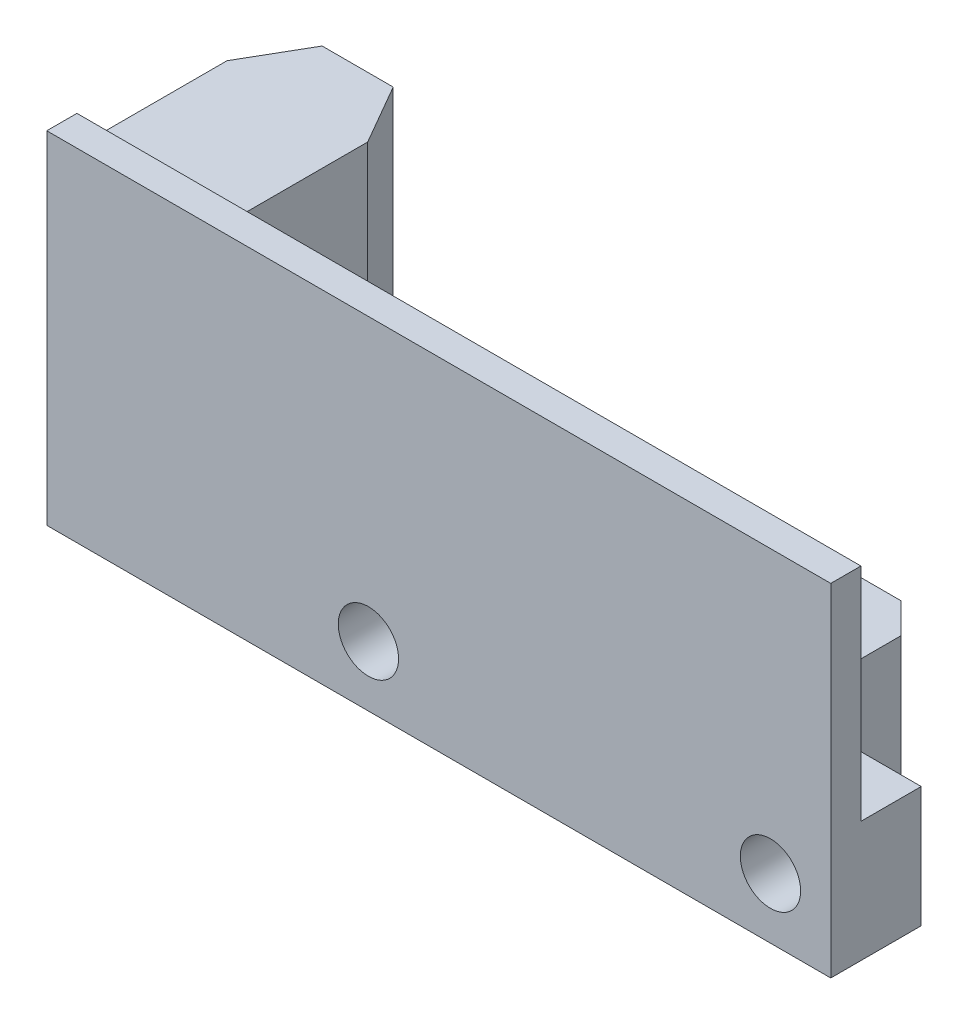
SolidWorks part; units mm, degrees
ref_plane "Plan de face" through (0, 0, 0) normal (0, 0, 1) x (1, 0, 0)
ref_plane "Plan de dessus" through (0, 0, 0) normal (0, 1, 0) x (1, 0, 0)
ref_plane "Plan de droite" through (0, 0, 0) normal (1, 0, 0) x (0, 0, -1)
sketch "Esquisse1" plane through (0, 0, 0) normal (0, 0, 1) x (1, 0, 0)
  line L1 (-19.5, 8.5) -> (19.5, 8.5)
  line L2 (-19.5, 8.5) -> (-19.5, -8.5)
  line L3 (-19.5, -8.5) -> (19.5, -8.5)
  line L4 (19.5, 8.5) -> (19.5, -8.5)
  line L5 (-19.5, 8.5) -> (19.5, -8.5) construction
  line L6 (-19.5, -8.5) -> (19.5, 8.5) construction
  point P0 (0, 0)
  dimension "D1" = 39
  dimension "D2" = 17
extrude "Boss.-Extru.1" add sketch "Esquisse1" along normal blind 1.5
sketch "Esquisse3" plane through (0, -8.5, 0) normal (0, 1, 0) x (1, 0, 0)
  line L0 (19.5, 0) -> (19.5, 3)
  line L1 (19.5, 3) -> (12.5, 3)
  line L2 (12.5, 3) -> (12.5, 10.5)
  line L3 (12.5, 10.5) -> (8.5, 10.5)
  line L4 (8.5, 10.5) -> (8.5, 3)
  line L5 (8.5, 3) -> (5.5, 3)
  line L6 (5.5, 3) -> (5.5, 10.5)
  line L7 (5.5, 10.5) -> (1.5, 10.5)
  line L8 (1.5, 10.5) -> (1.5, 3)
  line L9 (1.5, 3) -> (-5.5, 3)
  line L10 (-5.5, 3) -> (-5.5, 0)
  line L11 (19.5, 0) -> (-19.5, 0) construction
  line L12 (-5.5, 0) -> (19.5, 0)
  dimension "D1" = 25
  dimension "D2" = 3
  dimension "D3" = 4
  dimension "D4" = 4
  dimension "D5" = 3
  dimension "D6" = 7
  dimension "D7" = 7
  dimension "D8" = 7.5
extrude "Boss.-Extru.2" add sketch "Esquisse3" along normal blind 6
sketch "Esquisse2" plane through (0, 0, 1.5) normal (0, 0, 1) x (1, 0, 0)
  line L0 (-3.5, -5.5) -> (16.5, -5.5) construction
  line L1 (19.5, -8.5) -> (19.5, 8.5) construction
  line L3 (-19.5, -8.5) -> (19.5, -8.5) construction
  circle A0 centre (16.5, -5.5) radius 1.5
  circle A1 centre (-3.5, -5.5) radius 1.5
  dimension "D1" = 3
  dimension "D2" = 3
  dimension "D3" = 3
  dimension "D4" = 20
extrude "Enlèv. mat.-Extru.1" cut sketch "Esquisse2" against normal through all
chamfer "Chanfrein1" distance 1.5 angle 45 1 edges at (12.5, -5.5, -10.5)
sketch "Esquisse4" plane through (0, 0, 0) normal (0, 0, -1) x (-1, 0, 0)
  line L0 (19.5, 0) -> (15.5342, 0) construction
  line L1 (19.0342, 7.5) -> (12.0342, 7.5)
  line L2 (19.0342, 7.5) -> (19.0342, -7.5)
  line L3 (19.0342, -7.5) -> (12.0342, -7.5)
  line L4 (12.0342, 7.5) -> (12.0342, -7.5)
  line L5 (19.0342, 7.5) -> (12.0342, -7.5) construction
  line L6 (19.0342, -7.5) -> (12.0342, 7.5) construction
  line L7 (19.5, 8.5) -> (19.5, -8.5) construction
  point P0 (15.5342, 0)
  dimension "D1" = 7
  dimension "D2" = 15
extrude "Boss.-Extru.3" add sketch "Esquisse4" along normal blind 10
chamfer "Chanfrein2" distance 3 angle 30 2 edges at (-19.0342, 0, -10) (-12.0342, 0, -10)
